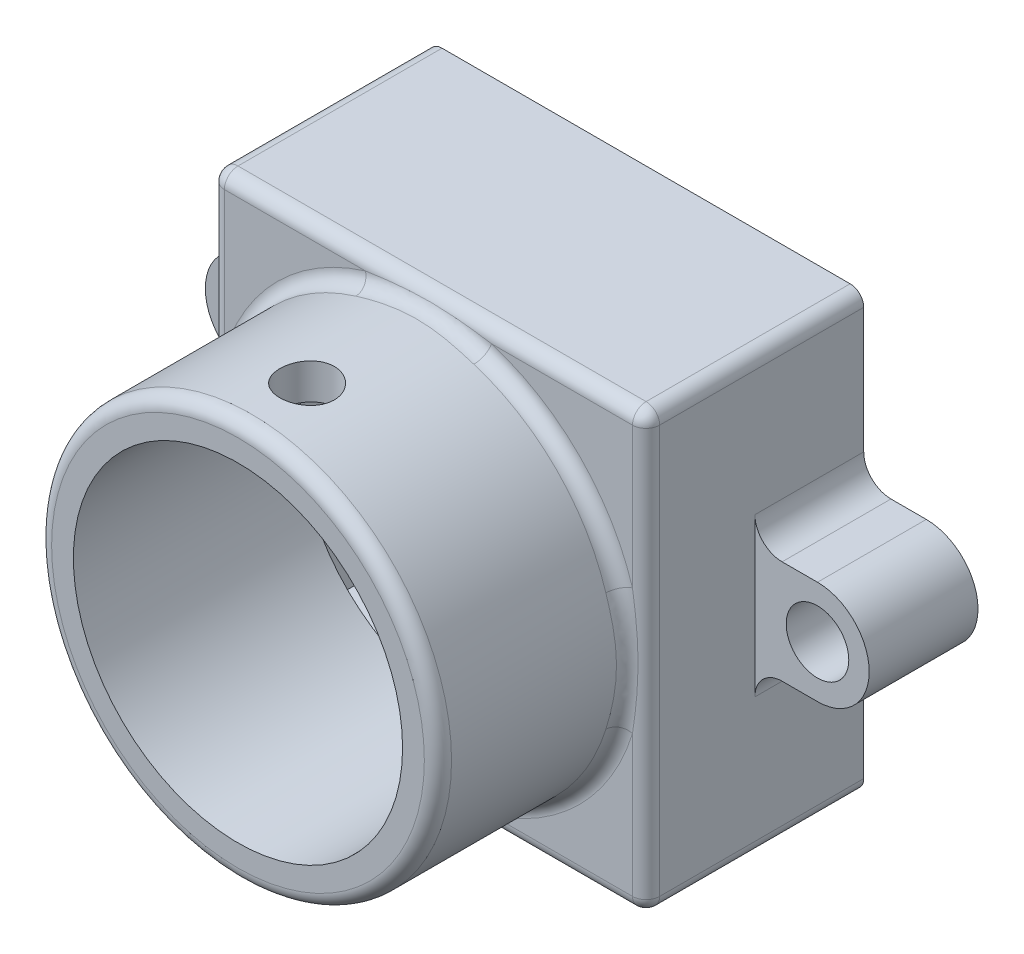
SolidWorks part; units mm, degrees
ref_plane "Front Plane" through (0, 0, 0) normal (0, 0, 1) x (1, 0, 0)
ref_plane "Top Plane" through (0, 0, 0) normal (0, 1, 0) x (1, 0, 0)
ref_plane "Right Plane" through (0, 0, 0) normal (1, 0, 0) x (0, 0, -1)
sketch "Sketch1" plane through (0, 0, 0) normal (0, 0, 1) x (1, 0, 0)
  line L0 (-8, 8) -> (8, -8) construction
  line L1 (-8, 8) -> (8, 8)
  line L2 (-8, 8) -> (-8, -8)
  line L3 (-8, -8) -> (8, -8)
  line L4 (8, 8) -> (8, -8)
  line L5 (-8, -8) -> (8, 8) construction
  dimension "D1" = 16
extrude "Extrude1" add sketch "Sketch1" along normal blind 8
sketch "Sketch2" plane through (0, 0, 8) normal (0, 0, 1) x (1, 0, 0)
  circle A0 centre (0, 0) radius 7.35
  dimension "D1" = 14.7
extrude "Extrude2" add sketch "Sketch2" along normal blind 7
sketch "screw_axis" plane through (0, 0, 0) normal (1, 0, 0) x (0, 0, -1)
  line L0 (-12.46, 10.8114) -> (-12.46, 0) construction
  line L1 (-15, 7.35) -> (-15, -7.35) construction
  dimension "D1" = 2.54
shell "Shell1" thickness 1.3
sketch "Sketch6" plane through (0, 0, 0) normal (0, 1, 0) x (1, 0, 0)
  circle A0 centre (0, -12.46) radius 1
  dimension "D1" = 2
extrude "Cut-Extrude1" cut sketch "Sketch6" along normal through all
sketch "Sketch4" plane through (0, 0, 0) normal (0, 0, 1) x (1, 0, 0)
  line L0 (-10.3, 0) -> (10.0674, 0) construction
  line L1 (-8, 8) -> (-8, -8) construction
  line L2 (-8, 1.9) -> (-10.3, 1.9)
  line L3 (-8, 1.9) -> (-8, -1.9)
  line L4 (-8, -1.9) -> (-10.3, -1.9)
  line L5 (-10.3, 1.9) -> (-10.3, -1.9) construction
  line L6 (-12.2, 4.4471) -> (-12.2, -5.1662) construction
  line L7 (0, 9.9349) -> (0, -12.6978) construction
  line L8 (8, 1.9) -> (8, -1.9)
  line L9 (8, -1.9) -> (10.3, -1.9)
  line L10 (8, 1.9) -> (10.3, 1.9)
  arc A0 (-10.3, -1.9) -> (-10.3, 1.9) centre (-10.3, 0) cw
  arc A1 (10.3, -1.9) -> (10.3, 1.9) centre (10.3, 0) ccw
  circle A2 centre (-10.3, 0) radius 1.15
  circle A3 centre (10.3, 0) radius 1.15
  dimension "D3" = 0.75
  dimension "D1" = 3.8
  dimension "D2" = 12.2
extrude "Extrude3" add sketch "Sketch4" along normal blind 4
fillet "Fillet1" radius 0.5 8 edges at (-8, 8, 4) (-8, -8, 4) (8, -8, 4) (8, 8, 4) (0, -8, 8) (-8, 0, 8) (0, 8, 8) (8, 0, 8)
fillet "Fillet2" radius 0.5 2 edges at (7.35, 0, 8) (7.35, 0, 15)
fillet "Fillet3" radius 1 4 edges
